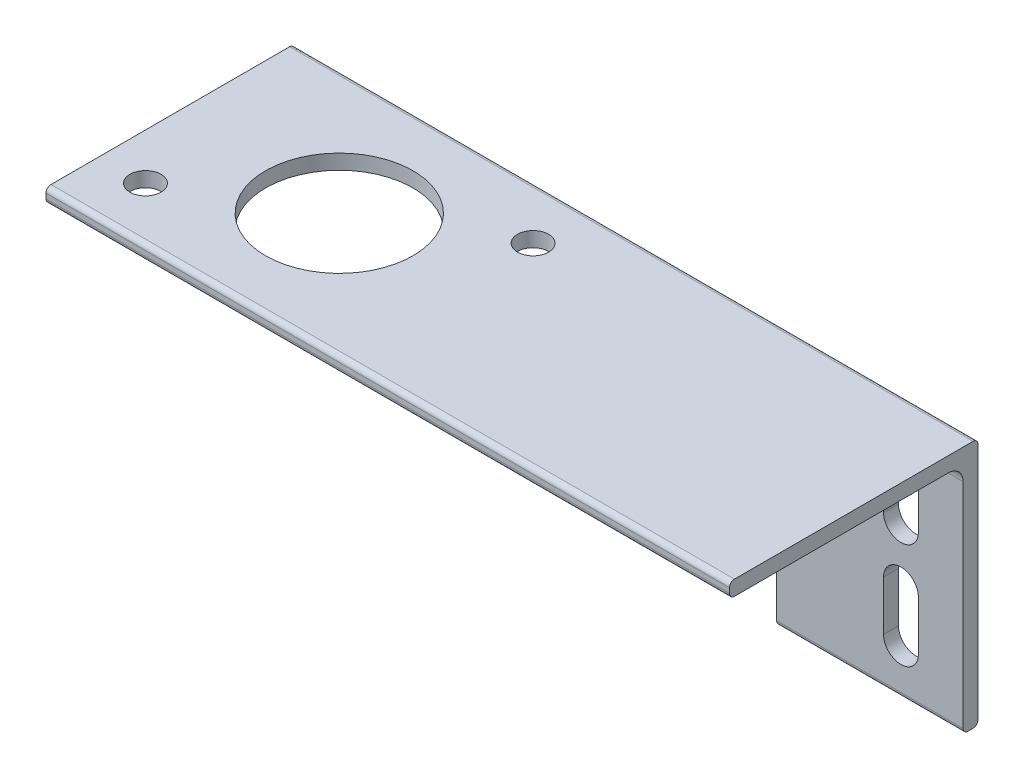
SolidWorks part; units mm, degrees
ref_plane "Front Plane" through (0, 0, 0) normal (0, 0, 1) x (1, 0, 0)
ref_plane "Top Plane" through (0, 0, 0) normal (0, 1, 0) x (1, 0, 0)
ref_plane "Right Plane" through (0, 0, 0) normal (1, 0, 0) x (0, 0, -1)
sketch "Sketch1" plane through (0, 0, 0) normal (1, 0, 0) x (0, 0, -1)
  line L0 (9.652, 11.176) -> (-11.176, 11.176)
  line L1 (12.192, 12.7) -> (-12.192, 12.7)
  line L2 (12.7, 12.192) -> (12.7, -12.192)
  line L3 (12.192, -12.7) -> (11.684, -12.7)
  line L4 (-12.7, 12.192) -> (-12.7, 11.684)
  line L9 (11.176, 9.652) -> (11.176, -11.176)
  line L10 (11.176, -11.176) -> (11.176, -12.192)
  line L11 (-11.176, 11.176) -> (-12.192, 11.176)
  arc A0 (11.176, -12.192) -> (11.684, -12.7) centre (11.684, -12.192) ccw
  arc A1 (12.7, -12.192) -> (12.192, -12.7) centre (12.192, -12.192) cw
  arc A2 (12.192, 12.7) -> (12.7, 12.192) centre (12.192, 12.192) cw
  arc A3 (-12.192, 11.176) -> (-12.7, 11.684) centre (-12.192, 11.684) cw
  arc A4 (-12.192, 12.7) -> (-12.7, 12.192) centre (-12.192, 12.192) ccw
  arc A5 (9.652, 11.176) -> (11.176, 9.652) centre (9.652, 9.652) cw
  point P0 (0, 0)
  point P1 (-12.7, -12.7)
  point P3 (12.7, -12.7)
  point P4 (-12.7, 12.7)
  point P18 (12.7, 12.7)
  dimension "D7" = 0.508
  dimension "D8" = 1.524
  dimension "D1" = 25.4
  dimension "D2" = 25.4
  dimension "D3" = 12.7
  dimension "D4" = 12.7
  dimension "D5" = 1.524
  dimension "D6" = 1.524
extrude "Boss-Extrude1" add sketch "Sketch1" along normal blind 69.85
sketch "Sketch2" plane through (0, 12.7, 0) normal (0, 1, 0) x (1, 0, 0)
  line L0 (0, 0) -> (69.85, 0) construction
  line L1 (0, 12.192) -> (0, -12.192) construction
  line L2 (69.85, 12.192) -> (69.85, -12.192) construction
  line L3 (4.7146, -7.25) -> (29.8294, 7.25) construction
  circle A0 centre (17.272, 0) radius 7.5311
  circle A2 centre (29.8294, 7.25) radius 1.5875
  circle A3 centre (4.7146, -7.25) radius 1.5875
  dimension "D2" = 15.0622
  dimension "D4" = 30
  dimension "D5" = 3.175
  dimension "D1" = 17.272
  dimension "D3" = 29
extrude "Cut-Extrude1" cut sketch "Sketch2" against normal through all
sketch "Sketch3" plane through (0, 0, -12.7) normal (0, 0, -1) x (-1, 0, 0)
  line L0 (-38.1, -2.6156) -> (0, -2.6156) construction
  line L1 (-38.1, 10.0844) -> (0, 10.0844)
  line L2 (-38.1, -15.3156) -> (0, -15.3156)
  line L4 (0, -12.192) -> (0, 12.192) construction
  line L5 (-50.8, -2.6156) -> (-50.8, -15.3156)
  line L6 (-50.8, -15.3156) -> (-38.1, -15.3156)
  arc A0 (-38.1, 10.0844) -> (-50.8, -2.6156) centre (-38.1, -2.6156) ccw
  arc A1 (0, -15.3156) -> (0, 10.0844) centre (0, -2.6156) ccw
  point P2 (-19.05, -2.6156)
  dimension "D2" = 12.7
  dimension "D1" = 38.1
  dimension "D3" = 38.1
extrude "Cut-Extrude2" cut sketch "Sketch3" against normal through all
sketch "Sketch4" plane through (0, 0, -12.7) normal (0, 0, -1) x (-1, 0, 0)
  line L0 (-63.5, -7.9375) -> (-63.5, -2.8575) construction
  line L1 (-65.278, -7.9375) -> (-65.278, -2.8575)
  line L2 (-61.722, -7.9375) -> (-61.722, -2.8575)
  line L3 (-63.5, 2.8575) -> (-63.5, 7.9375) construction
  line L4 (-65.278, 2.8575) -> (-65.278, 7.9375)
  line L5 (-61.722, 2.8575) -> (-61.722, 7.9375)
  line L6 (-69.85, -12.7) -> (-50.8, -12.7) construction
  line L7 (-69.85, 12.7) -> (0, 12.7) construction
  line L8 (-69.85, -12.192) -> (-69.85, 12.192) construction
  arc A0 (-65.278, -7.9375) -> (-61.722, -7.9375) centre (-63.5, -7.9375) ccw
  arc A1 (-61.722, -2.8575) -> (-65.278, -2.8575) centre (-63.5, -2.8575) ccw
  arc A2 (-65.278, 2.8575) -> (-61.722, 2.8575) centre (-63.5, 2.8575) ccw
  arc A3 (-61.722, 7.9375) -> (-65.278, 7.9375) centre (-63.5, 7.9375) ccw
  point P2 (-63.5, -5.3975)
  point P9 (-63.5, 5.3975)
  dimension "D1" = 1.778
  dimension "D2" = 1.778
  dimension "D3" = 4.7625
  dimension "D4" = 4.7625
  dimension "D5" = 5.08
  dimension "D6" = 5.08
  dimension "D7" = 6.35
extrude "Cut-Extrude3" cut sketch "Sketch4" against normal through all
